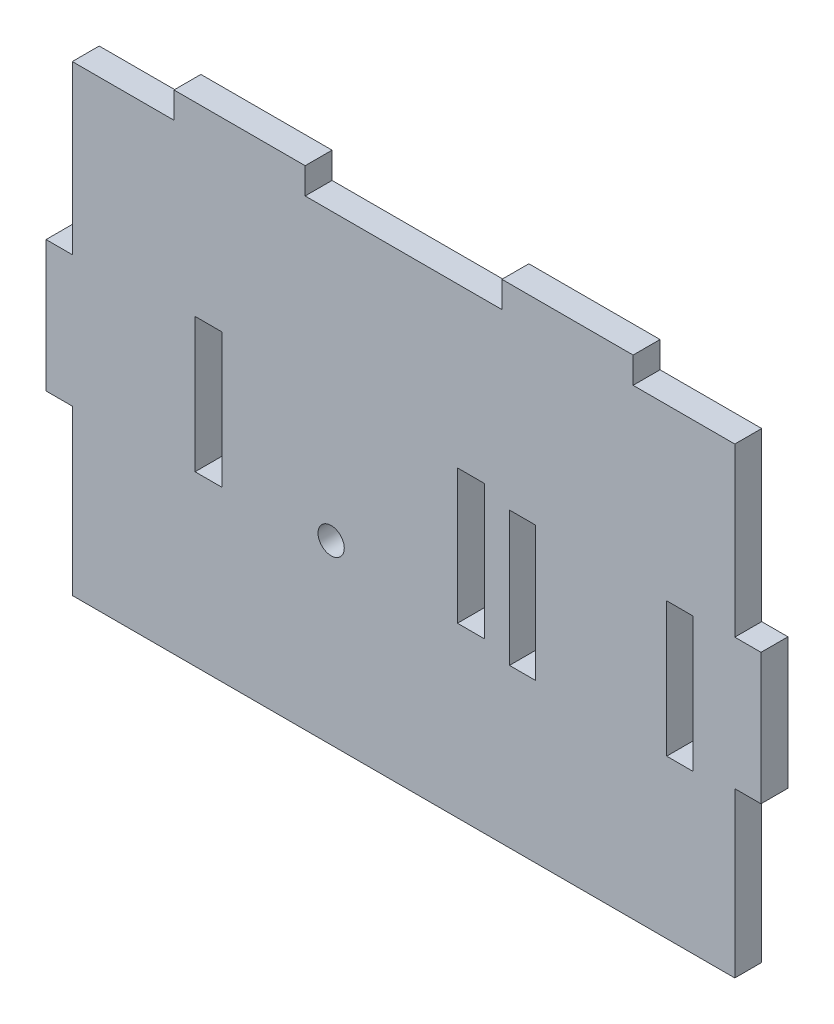
SolidWorks part; units mm, degrees
ref_plane "Alzado" through (0, 0, 0) normal (0, 0, 1) x (1, 0, 0)
ref_plane "Planta" through (0, 0, 0) normal (0, 1, 0) x (1, 0, 0)
ref_plane "Vista lateral" through (0, 0, 0) normal (1, 0, 0) x (0, 0, -1)
sketch "Croquis1" plane through (0, 0, 0) normal (0, 0, 1) x (1, 0, 0)
  line L0 (1.5261, 36.2344) -> (1.5261, 45.9842)
  line L1 (1.5261, 45.9842) -> (5.426, 45.9842)
  line L2 (1.5261, 36.2344) -> (1.5261, 26.4846)
  line L3 (1.5261, 26.4846) -> (5.426, 26.4846)
  line L4 (20.5381, 70.8461) -> (20.5381, 74.7461)
  line L5 (20.5381, 74.7461) -> (40.0377, 74.7461)
  line L6 (40.0377, 74.7461) -> (40.0377, 70.8461)
  line L7 (88.7866, 70.8461) -> (88.7866, 74.7461)
  line L8 (88.7866, 74.7461) -> (69.2871, 74.7461)
  line L9 (69.2871, 74.7461) -> (69.2871, 70.8461)
  line L10 (107.7987, 36.2344) -> (107.7987, 45.9842)
  line L11 (107.7987, 45.9842) -> (103.8988, 45.9842)
  line L12 (107.7987, 36.2344) -> (107.7987, 26.4846)
  line L13 (107.7987, 26.4846) -> (103.8988, 26.4846)
  line L14 (88.7866, 70.8461) -> (103.8988, 70.8461)
  line L15 (103.8988, 70.8461) -> (103.8988, 45.9842)
  line L16 (40.0377, 70.8461) -> (69.2871, 70.8461)
  line L17 (5.426, 45.9842) -> (5.426, 70.8461)
  line L18 (5.426, 70.8461) -> (20.5381, 70.8461)
  line L19 (5.426, 26.4846) -> (5.426, 2.1101)
  line L20 (103.8988, 2.1101) -> (103.8988, 26.4846)
  line L21 (5.426, 2.1101) -> (103.8988, 2.1101)
  line L22 (70.4072, 45.6039) -> (74.3071, 45.6039)
  line L23 (74.3071, 45.6039) -> (74.3071, 25.6039)
  line L24 (74.3071, 25.6039) -> (70.4072, 25.6039)
  line L25 (70.4072, 25.6039) -> (70.4072, 45.6039)
  line L27 (93.7747, 45.6039) -> (97.7066, 45.6039)
  line L28 (97.7066, 45.6039) -> (97.7066, 25.6039)
  line L29 (97.7066, 25.6039) -> (93.7747, 25.6039)
  line L31 (93.7747, 45.6039) -> (93.7747, 25.6039)
  line L32 (97.7066, 35.6039) -> (63.4803, 35.6039) construction
  circle A0 centre (43.9029, 28.4112) radius 1.95
  point P33 (74.3071, 35.6039)
  point P38 (70.4072, 35.6039)
  dimension "D1" = 20
  dimension "D2" = 20
  dimension "D3" = 20
extrude "Saliente-Extruir1" add sketch "Croquis1" along normal blind 4
sketch "Croquis3" plane through (0, 0, 4) normal (0, 0, 1) x (1, 0, 0)
  line L0 (62.6741, 37.1643) -> (27.6741, 37.1643) construction
  line L1 (62.6741, 47.1643) -> (66.6741, 47.1643)
  line L2 (62.6741, 47.1643) -> (62.6741, 27.1643)
  line L3 (62.6741, 27.1643) -> (66.6741, 27.1643)
  line L4 (66.6741, 47.1643) -> (66.6741, 27.1643)
  line L5 (45.1741, 37.1643) -> (45.1741, 45.8294) construction
  line L6 (27.6741, 27.1643) -> (23.6741, 27.1643)
  line L7 (23.6741, 47.1643) -> (23.6741, 27.1643)
  line L8 (27.6741, 47.1643) -> (23.6741, 47.1643)
  line L9 (27.6741, 47.1643) -> (27.6741, 27.1643)
  point P8 (62.6741, 37.1643)
  dimension "D1" = 4
  dimension "D2" = 20
  dimension "D3" = 35
extrude "Cortar-Extruir2" cut sketch "Croquis3" against normal blind 18
